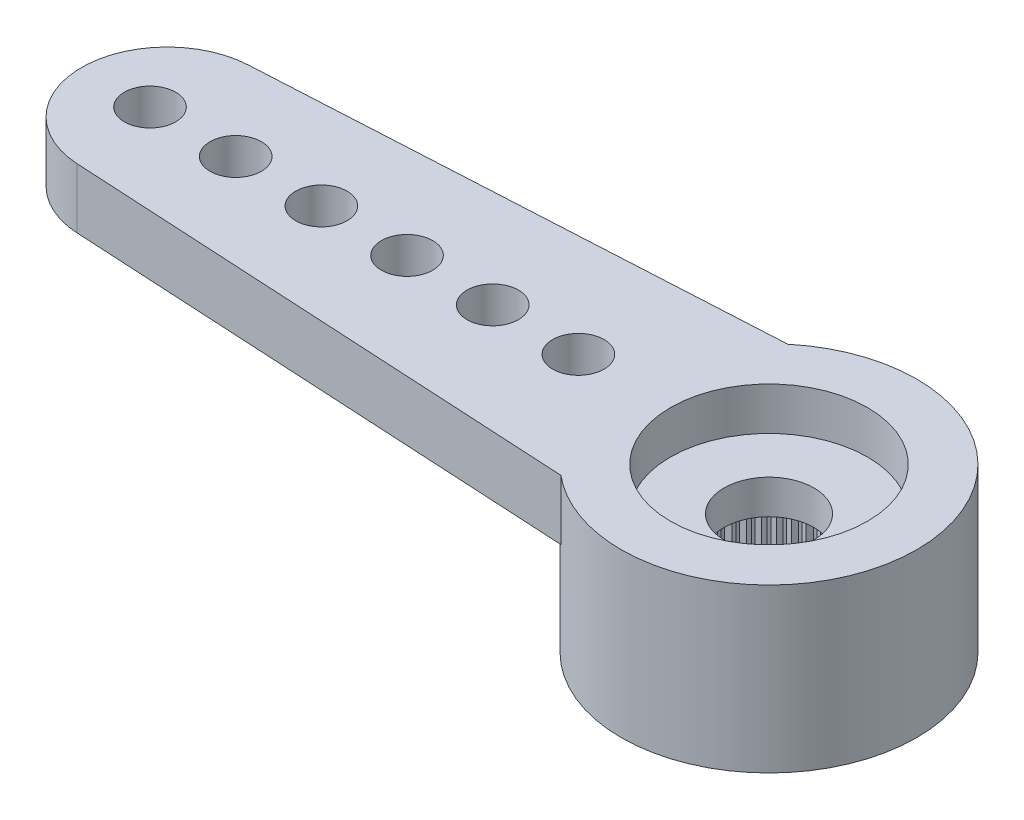
SolidWorks part; units mm, degrees
material "PVC Rígido"
ref_plane "Plano frontal" through (0, 0, 0) normal (0, 0, 1) x (1, 0, 0)
ref_plane "Plano superior" through (0, 0, 0) normal (0, 1, 0) x (1, 0, 0)
ref_plane "Plano direito" through (0, 0, 0) normal (1, 0, 0) x (0, 0, -1)
sketch "Esboço1" plane through (0, 0, 0) normal (0, 1, 0) x (1, 0, 0)
  line L0 (0, 0) -> (-14.05, 0) construction
  line L1 (-14.1591, 1.997) -> (-2.2091, 2.65)
  line L2 (-2.2091, -2.65) -> (-14.1591, -1.997)
  arc A0 (-2.2091, -2.65) -> (-2.2091, 2.65) centre (0, 0) ccw
  arc A1 (-14.1591, 1.997) -> (-14.1591, -1.997) centre (-14.05, 0) ccw
  dimension "D1" = 6.9
  dimension "D2" = 4
  dimension "D3" = 19.5
  dimension "D4" = 5.3
extrude "Ressalto-extrusão1" add sketch "Esboço1" against normal blind 1.4
sketch "Esboço2" plane through (0, -1.4, 0) normal (0, -1, 0) x (1, 0, 0)
  arc A0 (-2.2091, -2.65) -> (-2.2091, 2.65) centre (0, 0) ccw construction
  circle A1 centre (0, 0) radius 3.45
extrude "Ressalto-extrusão2" add sketch "Esboço2" along normal offset from surface (2.4 mm away) 3.8 up to face at (-7.242, 0, 0)
hole_wizard "Furo4" positions "Esboço9" profile "Esboço10" legacy end condition through all
sketch "Esboço9" plane through (0, 0, 0) normal (0, 1, 0) x (1, 0, 0)
  line L1 (-14.45, 0) -> (0, 0) construction
  arc A2 (-14.1591, 1.997) -> (-14.1591, -1.997) centre (-14.05, 0) ccw construction
  point P0 (-14.45, 0)
  point P19 (-16.05, 0)
  dimension "D1" = 1.6
sketch "Esboço10" plane through (-14.45, 0, 0) normal (1, 0, 0) x (0, 0, 1)
  line L0 (0, 0) -> (0, 3.8)
  line L1 (0, 3.8) -> (0.6, 3.8)
  line L2 (0.6, 3.8) -> (0.6, 0)
  line L3 (0.6, 0) -> (0, 0)
  line L4 (0, 110) -> (0, -10) construction
  dimension "Diameter" = 1.2
  dimension "Depth" = 3.8
pattern_linear "Padrão linear1" count 6 spacing 2 along (1, 0, 0) of "Furo4"
hole_wizard "Furo1" positions "Esboço3" profile "Esboço4" legacy
sketch "Esboço3" plane through (0, -3.8, 0) normal (0, -1, 0) x (-1, 0, 0)
  point P0 (0, 0)
sketch "Esboço4" plane through (0, -3.8, 0) normal (1, 0, 0) x (0, 0, -1)
  line L0 (0, 0) -> (0, 2)
  line L1 (0, 2) -> (2.475, 2)
  line L2 (2.475, 2) -> (2.475, 0)
  line L3 (2.475, 0) -> (0, 0)
  line L4 (0, 110) -> (0, -10) construction
  dimension "Diameter" = 4.95
  dimension "Depth" = 2
hole_wizard "Furo2" positions "Esboço5" profile "Esboço6" legacy
sketch "Esboço5" plane through (0, 0, 0) normal (0, 1, 0) x (1, 0, 0)
  point P0 (0, 0)
sketch "Esboço6" plane through (0, 0, 0) normal (1, 0, 0) x (0, 0, 1)
  line L0 (0, 0) -> (0, 1)
  line L1 (0, 1) -> (2.3, 1)
  line L2 (2.3, 1) -> (2.3, 0)
  line L3 (2.3, 0) -> (0, 0)
  line L4 (0, 110) -> (0, -10) construction
  dimension "Diameter" = 4.6
  dimension "Depth" = 1
hole_wizard "Furo3" positions "Esboço7" profile "Esboço8" legacy end condition through all
sketch "Esboço7" plane through (0, 0, 0) normal (0, 1, 0) x (1, 0, 0)
  point P0 (0, 0)
sketch "Esboço8" plane through (0, 0, 0) normal (1, 0, 0) x (0, 0, 1)
  line L0 (0, 0) -> (0, 3.8)
  line L1 (0, 3.8) -> (1.05, 3.8)
  line L2 (1.05, 3.8) -> (1.05, 0)
  line L3 (1.05, 0) -> (0, 0)
  line L4 (0, 110) -> (0, -10) construction
  dimension "Diameter" = 2.1
  dimension "Depth" = 3.8
sketch "Esboço11" plane through (0, -3.8, 0) normal (0, -1, 0) x (1, 0, 0)
  line L0 (-0.0981, 2.4731) -> (0, 2.375)
  line L1 (0, 2.375) -> (0.0981, 2.4731)
  line L2 (0, 0) -> (0, 2.475) construction
  circle A0 centre (0, 0) radius 2.375 construction
  circle A1 centre (0, 0) radius 2.475
  arc A2 (0.0981, 2.4731) -> (-0.0981, 2.4731) centre (0, 0) ccw
  dimension "D3" = 4.75
  dimension "D2" = 0.1
  dimension "D1" = 0
extrude "Ressalto-extrusão3" add sketch "Esboço11" against normal up to surface (2 mm away) up to face at (0, -1.8, 1.05)
pattern_circular "PadrãoCircular1" count 60 over 360 about axis through (0, 0, 0) along (0, 1, 0) of "Ressalto-extrusão3"
